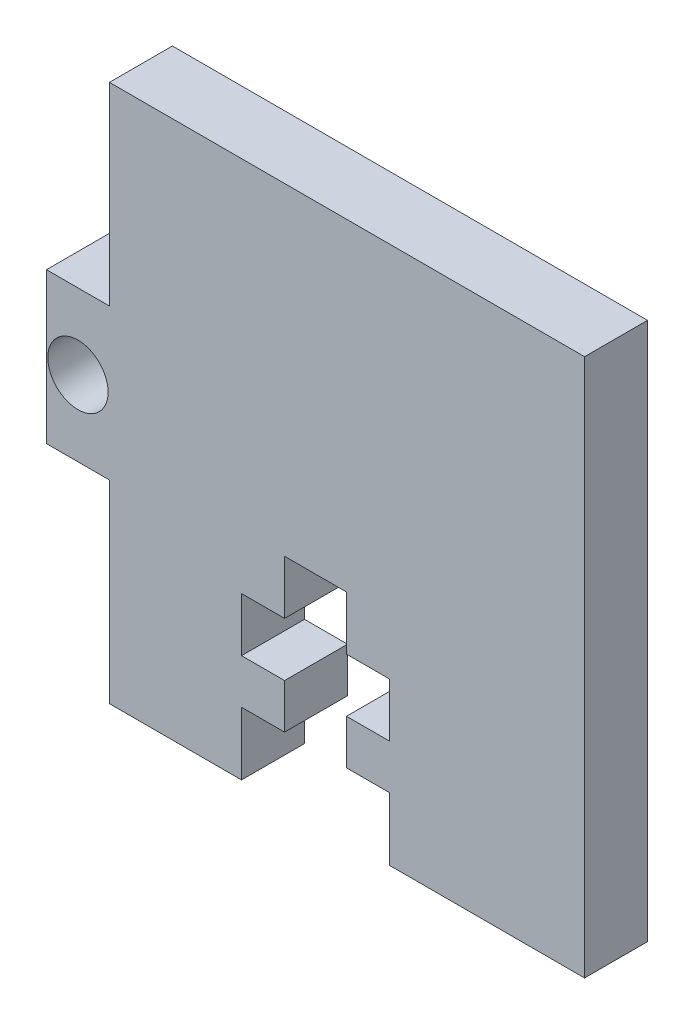
SolidWorks part; units mm, degrees
ref_plane "Front Plane" through (0, 0, 0) normal (0, 0, 1) x (1, 0, 0)
ref_plane "Top Plane" through (0, 0, 0) normal (0, 1, 0) x (1, 0, 0)
ref_plane "Right Plane" through (0, 0, 0) normal (1, 0, 0) x (0, 0, -1)
sketch "Sketch1" plane through (0, 0, 0) normal (0, 0, 1) x (1, 0, 0)
  line L0 (2.9718, 25.4) -> (2.9718, 16.256)
  line L1 (0, 0) -> (25.4, 0)
  line L2 (0, 0) -> (0, 25.4)
  line L3 (0, 25.4) -> (25.4, 25.4)
  line L4 (25.4, 0) -> (25.4, 25.4)
  line L5 (2.9718, 16.256) -> (0, 16.256)
  line L6 (0, 16.256) -> (0, 9.144)
  line L7 (0, 9.144) -> (2.9718, 9.144)
  line L8 (2.9718, 9.144) -> (2.9718, 0)
  line L9 (25.4, 0) -> (0, 0)
  line L11 (12.7, 25.4) -> (12.7, 0) construction
  line L12 (9.2075, 0) -> (9.2075, 2.9718)
  line L13 (9.2075, 2.9718) -> (11.2395, 2.9718)
  line L14 (11.2395, 2.9718) -> (11.2395, 5.08)
  line L15 (11.2395, 5.08) -> (9.2075, 5.08)
  line L16 (9.2075, 5.08) -> (9.2075, 7.62)
  line L17 (9.2075, 7.62) -> (11.2395, 7.62)
  line L18 (11.2395, 7.62) -> (11.2395, 10.16)
  line L19 (11.2395, 10.16) -> (14.1605, 10.16)
  line L20 (16.1925, 0) -> (16.1925, 2.9718)
  line L21 (16.1925, 2.9718) -> (14.1605, 2.9718)
  line L22 (14.1605, 2.9718) -> (14.1605, 5.08)
  line L23 (14.1605, 5.08) -> (16.1925, 5.08)
  line L24 (16.1925, 5.08) -> (16.1925, 7.62)
  line L25 (16.1925, 7.62) -> (14.1605, 7.62)
  line L26 (14.1605, 7.62) -> (14.1605, 10.16)
  circle A0 centre (1.4859, 12.7) radius 1.4224
  point P14 (0, 12.7)
  point P18 (12.7, 0)
  point P37 (12.7, 10.16)
  dimension "D6" = 2.8448
  dimension "D8" = 1.4605
  dimension "D1" = 25.4
  dimension "D2" = 25.4
  dimension "D3" = 7.112
  dimension "D4" = 2.9718
  dimension "D5" = 9.144
  dimension "D7" = 1.4859
  dimension "D9" = 10.16
  dimension "D10" = 2.9718
  dimension "D11" = 3.4925
  dimension "D12" = 2.54
  dimension "D13" = 5.08
extrude "Boss-Extrude1" add sketch "Sketch1" along normal blind 2.9718 contours L11 L3 L0 L5 L2 L7 L8 L1 L12 L13 L14 L15 L16 L17 L18 L19 A0 | L3 L11 L19 L26 L25 L24 L23 L22 L21 L20 L1 L4
